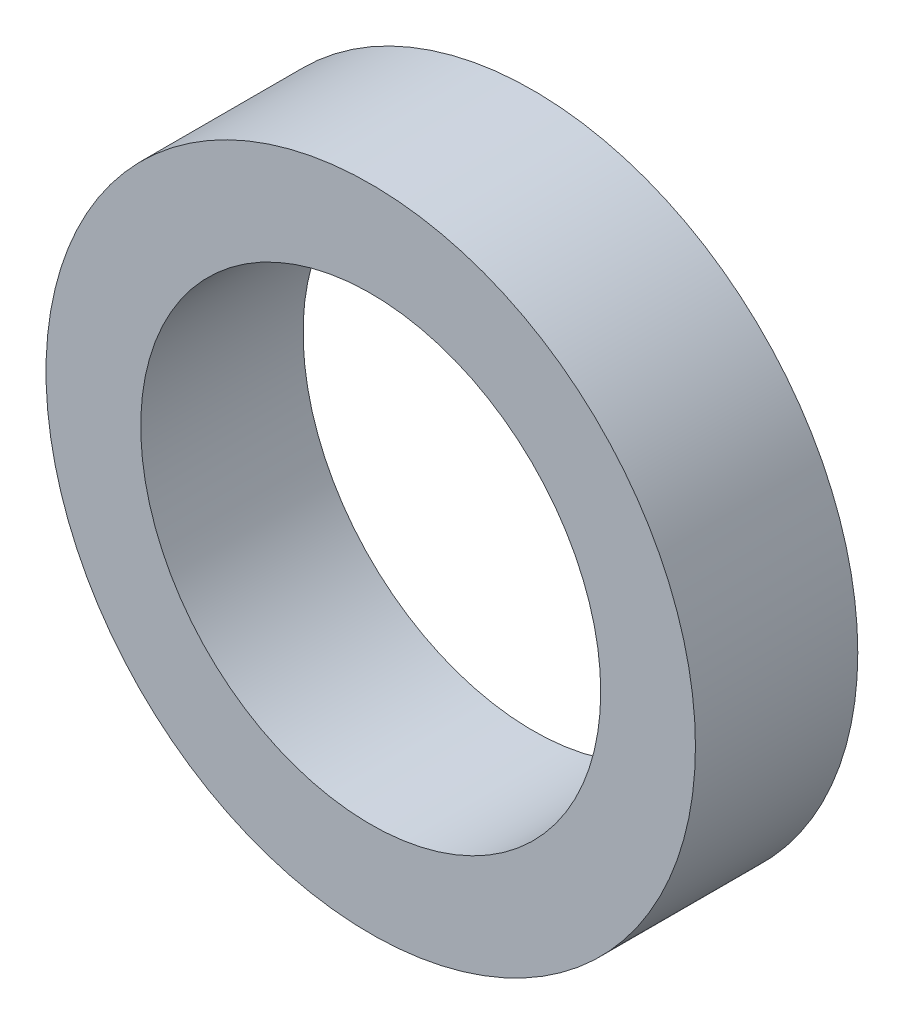
SolidWorks part; units mm, degrees
ref_plane "Plan de face" through (0, 0, 0) normal (0, 0, 1) x (1, 0, 0)
ref_plane "Plan de dessus" through (0, 0, 0) normal (0, 1, 0) x (1, 0, 0)
ref_plane "Plan de droite" through (0, 0, 0) normal (1, 0, 0) x (0, 0, -1)
sketch "Esquisse1" plane through (0, 0, 0) normal (0, 0, 1) x (1, 0, 0)
  circle A0 centre (0, 0) radius 6
  circle A1 centre (0, 0) radius 4.25
  dimension "D1" = 8.5
  dimension "D2" = 12
extrude "Boss.-Extru.1" add sketch "Esquisse1" along normal blind 3
